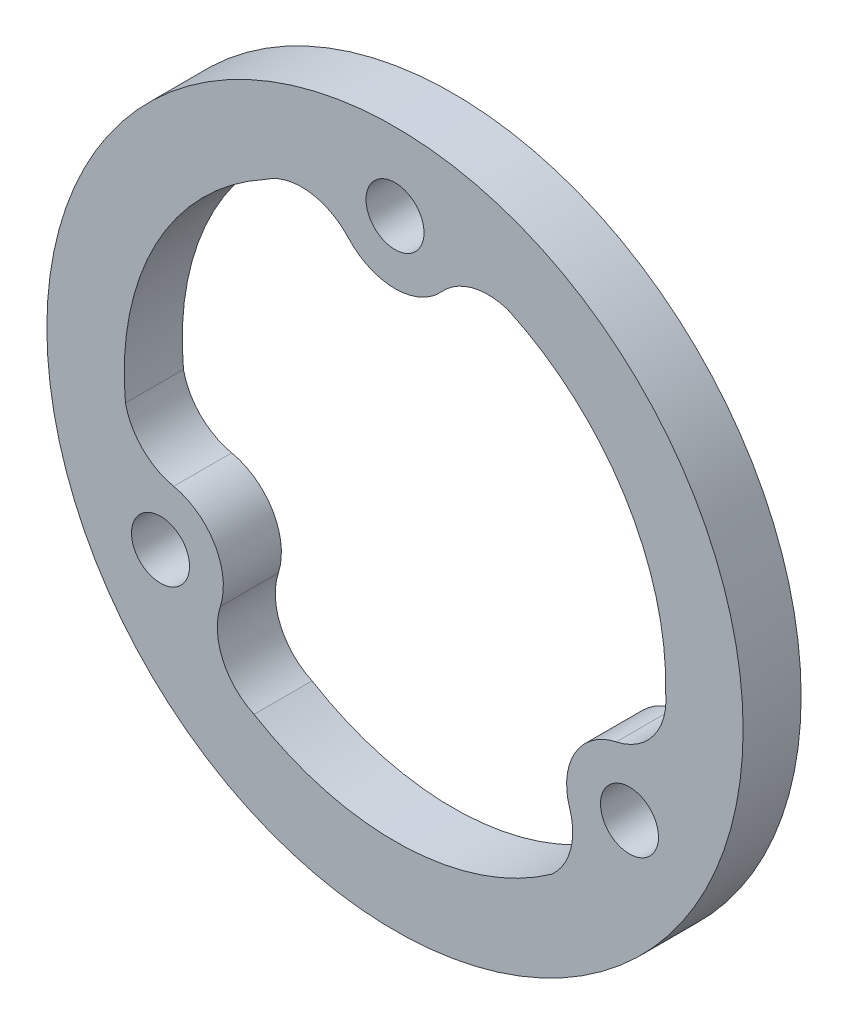
SolidWorks part; units mm, degrees
ref_plane "Plan de face" through (0, 0, 0) normal (0, 0, 1) x (1, 0, 0)
ref_plane "Plan de dessus" through (0, 0, 0) normal (0, 1, 0) x (1, 0, 0)
ref_plane "Plan de droite" through (0, 0, 0) normal (1, 0, 0) x (0, 0, -1)
sketch "Esquisse1" plane through (0, 0, 0) normal (0, 0, 1) x (1, 0, 0)
  line L0 (0, 14) -> (-12.125, -7.0011) construction
  line L1 (-12.125, -7.0011) -> (12.125, -7.0011) construction
  line L2 (12.125, -7.0011) -> (0, 14) construction
  circle A0 centre (0, 0) radius 18
  circle A2 centre (0, 14) radius 1.5
  arc A12 (-2.411, 11.8207) -> (2.411, 11.8207) centre (0, 14) ccw
  arc A16 (5.8094, 12.7378) -> (2.411, 11.8207) centre (4.8221, 9.6414) ccw
  arc A17 (-2.411, 11.8207) -> (-6.7074, 12.2887) centre (-4.8221, 9.6414) ccw
  arc A18 (-6.7074, 12.2887) -> (-13.9359, -1.3378) centre (0, 0) ccw
  arc A19 (8.1265, -11.4) -> (9.0315, -7.9984) centre (5.9386, -8.9967) ccw
  arc A20 (11.4425, -3.8223) -> (9.0315, -7.9984) centre (12.1244, -7) ccw
  arc A21 (11.4425, -3.8223) -> (13.996, -0.3356) centre (10.7607, -0.6447) ccw
  circle A22 centre (12.1244, -7) radius 1.5
  arc A23 (-13.9359, -1.3378) -> (-11.4425, -3.8223) centre (-10.7607, -0.6447) ccw
  arc A24 (-9.0315, -7.9984) -> (-11.4425, -3.8223) centre (-12.1244, -7) ccw
  arc A25 (-9.0315, -7.9984) -> (-7.2886, -11.9531) centre (-5.9386, -8.9967) ccw
  circle A26 centre (-12.1244, -7) radius 1.5
  arc A27 (-7.2886, -11.9531) -> (8.1265, -11.4) centre (0, 0) ccw
  arc A28 (13.996, -0.3356) -> (5.8094, 12.7378) centre (0, 0) ccw
  circle A29 centre (0, 14) radius 3.25 construction
  point P31 (0, 0)
  dimension "D1" = 36
  dimension "D2" = 3
  dimension "D3" = 3
  dimension "D4" = 6.5
  dimension "D5" = 14
  dimension "D8" = 14
  dimension "D9" = 3.25
  dimension "D10" = 14
  dimension "D11" = 3.25
  dimension "D12" = 24.25
  dimension "D13" = 24.25
  dimension "D6" = 60
  dimension "D7" = 60
  dimension "D14" = 10.78
  dimension "D15" = 10.78
extrude "Boss.-Extru.2" add sketch "Esquisse1" along normal blind 3
